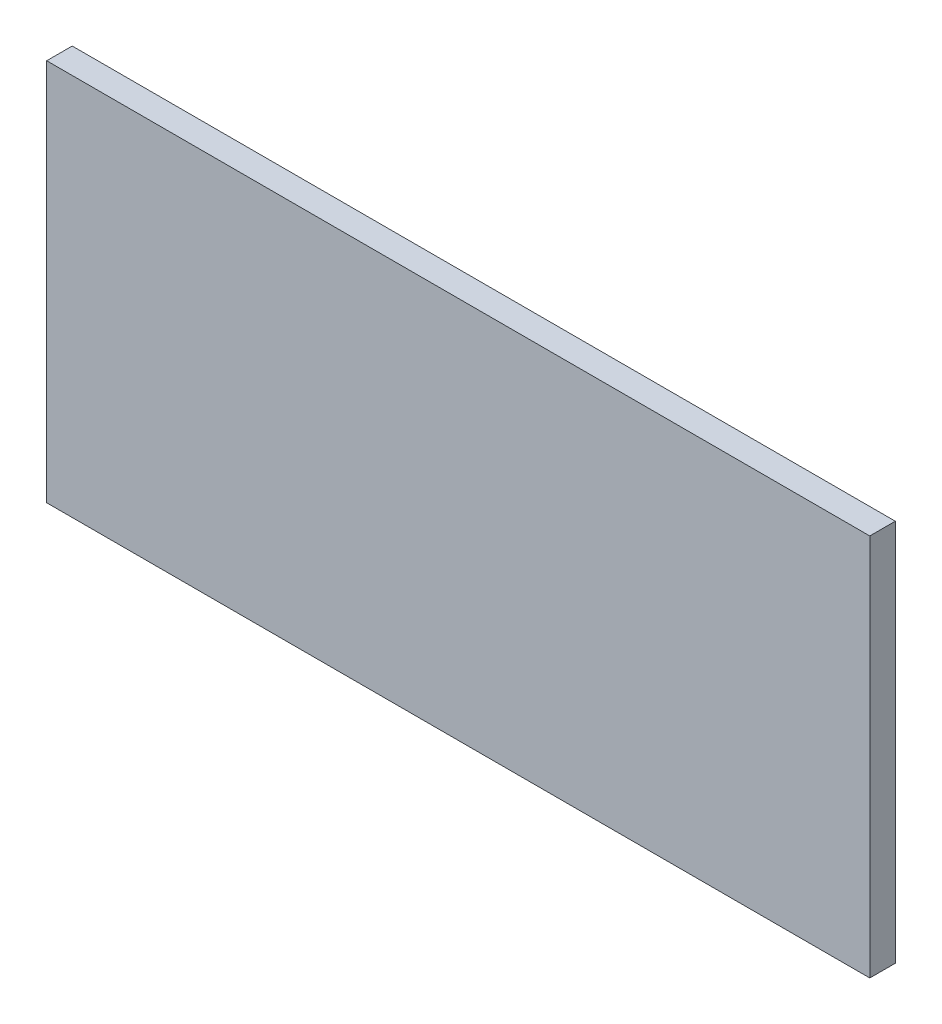
SolidWorks part; units mm, degrees
ref_plane "Alzado" through (0, 0, 0) normal (0, 0, 1) x (1, 0, 0)
ref_plane "Planta" through (0, 0, 0) normal (0, 1, 0) x (1, 0, 0)
ref_plane "Vista lateral" through (0, 0, 0) normal (1, 0, 0) x (0, 0, -1)
sketch "Croquis1" plane through (0, 0, 0) normal (0, 0, 1) x (1, 0, 0)
  line L1 (-356.8699, 239.7066) -> (288.1301, 239.7066)
  line L2 (-356.8699, 239.7066) -> (-356.8699, -60.2934)
  line L3 (-356.8699, -60.2934) -> (288.1301, -60.2934)
  line L4 (288.1301, 239.7066) -> (288.1301, -60.2934)
  dimension "D1" = 645
  dimension "D2" = 300
extrude "Saliente-Extruir1" add sketch "Croquis1" along normal blind 20
